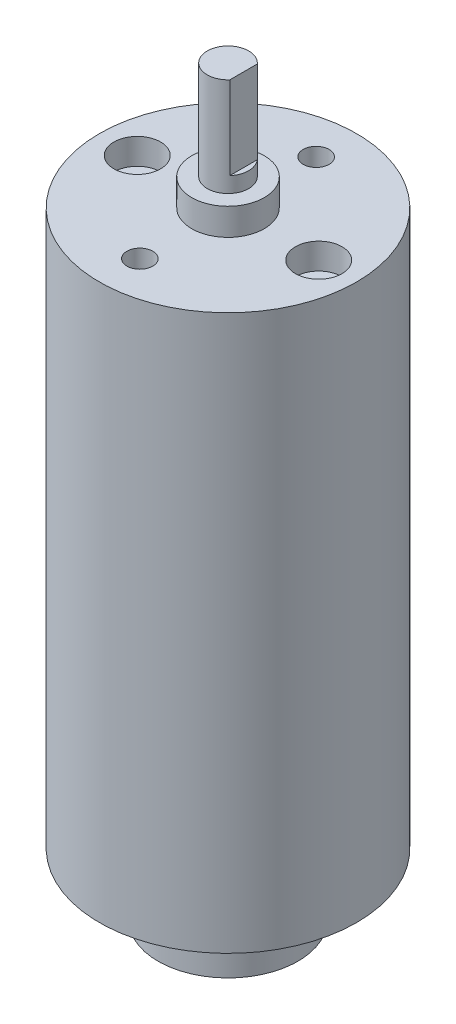
SolidWorks part; units mm, degrees
ref_plane "Alzado" through (0, 0, 0) normal (0, 0, 1) x (1, 0, 0)
ref_plane "Planta" through (0, 0, 0) normal (0, 1, 0) x (1, 0, 0)
ref_plane "Vista lateral" through (0, 0, 0) normal (1, 0, 0) x (0, 0, -1)
sketch "Croquis2" plane through (0, 0, 0) normal (0, 0, 1) x (1, 0, 0)
  line L0 (0, 0) -> (1, 0)
  line L1 (1, 0) -> (1, 2.05)
  line L2 (1, 2.05) -> (6.75, 2.05)
  line L3 (6.75, 2.05) -> (6.75, 6.05)
  line L4 (6.75, 6.05) -> (1, 6.05)
  line L5 (1, 6.05) -> (1, 8.1)
  line L6 (1, 8.1) -> (12.4, 8.1)
  line L7 (12.4, 8.1) -> (12.4, 61.6)
  line L8 (12.4, 61.6) -> (3.5, 61.6)
  line L9 (3.5, 61.6) -> (3.5, 64.2)
  line L10 (3.5, 64.2) -> (2, 64.2)
  line L11 (2, 64.2) -> (2, 73.7)
  line L12 (2, 73.7) -> (0, 73.7)
  line L13 (0, 73.7) -> (0, 0) construction
  line L14 (0, 0) -> (0, 73.7)
  point P2 (1, 1.025)
  dimension "D1" = 1
  dimension "D2" = 2.05
  dimension "D4" = 0
  dimension "D5" = 4
  dimension "D3" = 6.75
  dimension "D6" = 0
  dimension "D7" = 2.05
  dimension "D8" = 12.4
  dimension "D9" = 0
  dimension "D10" = 53.5
  dimension "D11" = 0
  dimension "D12" = 2
  dimension "D13" = 3.5
  dimension "D14" = 12.1
  dimension "D15" = 2.6
revolve "Revolución1" add sketch "Croquis2" angle 360 about L13
sketch "Croquis3" plane through (0, 61.6, 0) normal (0, 1, 0) x (1, 0, 0)
  circle A0 centre (0, 0) radius 8.75 construction
  circle A1 centre (0, 0) radius 12.4
  circle A2 centre (0, 0) radius 12.4
  circle A4 centre (8.75, 0) radius 2.25
  circle A5 centre (-8.75, 0) radius 2.25
  circle A7 centre (0, 0) radius 8.5 construction
  circle A8 centre (0, 8.5) radius 1.25
  circle A9 centre (0, -8.5) radius 1.25
  dimension "D2" = 17.5
  dimension "D3" = 4.5
  dimension "D4" = 2
  dimension "D5" = 2.5
  dimension "D6" = 17
  dimension "D1" = 0
  dimension "D7" = 2
extrude "Cortar-Extruir1" cut sketch "Croquis3" against normal blind 2.5 contours A4 | A5 | A9 | A8
sketch "Croquis4" plane through (0, 73.7, 0) normal (0, 1, 0) x (1, 0, 0)
  line L0 (1.5, 1.3229) -> (1.5, -1.3229)
  circle A1 centre (0, 0) radius 2
  circle A2 centre (0, 0) radius 2
  circle M3 centre (0, 0) radius 2
  dimension "D2" = 1.5
  dimension "D1" = 0
extrude "Cortar-Extruir2" cut sketch "Croquis4" against normal blind 8 contours L0 M3
sketch "Sketch4" plane through (1.5, 0, 0) normal (1, 0, 0) x (0, 0, -1)
  line L0 (0, 73.7) -> (0, 67.508)
  line L1 (1.3229, 73.7) -> (-1.3229, 73.7) construction
  line L2 (0, 13.64) -> (0, -13.64) construction
equation "\"D7@Croquis2\"=\"D2@Croquis2\""
